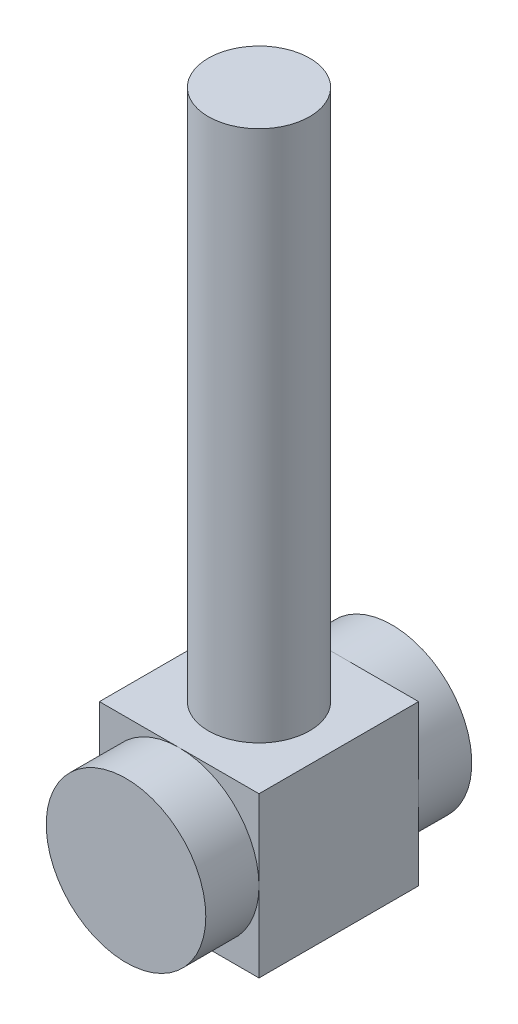
SolidWorks part; units mm, degrees
ref_plane "Front Plane" through (0, 0, 0) normal (0, 0, 1) x (1, 0, 0)
ref_plane "Top Plane" through (0, 0, 0) normal (0, 1, 0) x (1, 0, 0)
ref_plane "Right Plane" through (0, 0, 0) normal (1, 0, 0) x (0, 0, -1)
sketch "Sketch1" plane through (0, 0, 0) normal (0, 0, 1) x (1, 0, 0)
  line L1 (-15, 15) -> (15, 15)
  line L2 (-15, 15) -> (-15, -15)
  line L3 (-15, -15) -> (15, -15)
  line L4 (15, 15) -> (15, -15)
  line L5 (-15, 15) -> (15, -15) construction
  line L6 (-15, -15) -> (15, 15) construction
  point P0 (0, 0)
  dimension "D1" = 30
  dimension "D2" = 30
extrude "Boss-Extrude2" add sketch "Sketch1" along normal mid plane 30
sketch "Sketch2" plane through (0, 0, 15) normal (0, 0, 1) x (1, 0, 0)
  circle A0 centre (0, 0) radius 15
extrude "Boss-Extrude3" add sketch "Sketch2" along normal blind 10
sketch "Sketch3" plane through (0, 0, -15) normal (0, 0, -1) x (-1, 0, 0)
  circle A0 centre (0, 0) radius 15
extrude "Boss-Extrude4" add sketch "Sketch3" along normal blind 10
sketch "Sketch4" plane through (0, 15, 0) normal (0, 1, 0) x (1, 0, 0)
  circle A0 centre (0, 0) radius 9.5283
extrude "Cut-Extrude1" cut sketch "Sketch4" against normal through all
sketch "Sketch5" plane through (0, 15, 0) normal (0, 1, 0) x (1, 0, 0)
  circle A0 centre (0, 0) radius 9.5283
extrude "Boss-Extrude5" add sketch "Sketch5" along normal blind 130 from offset 30 offset against normal yes
